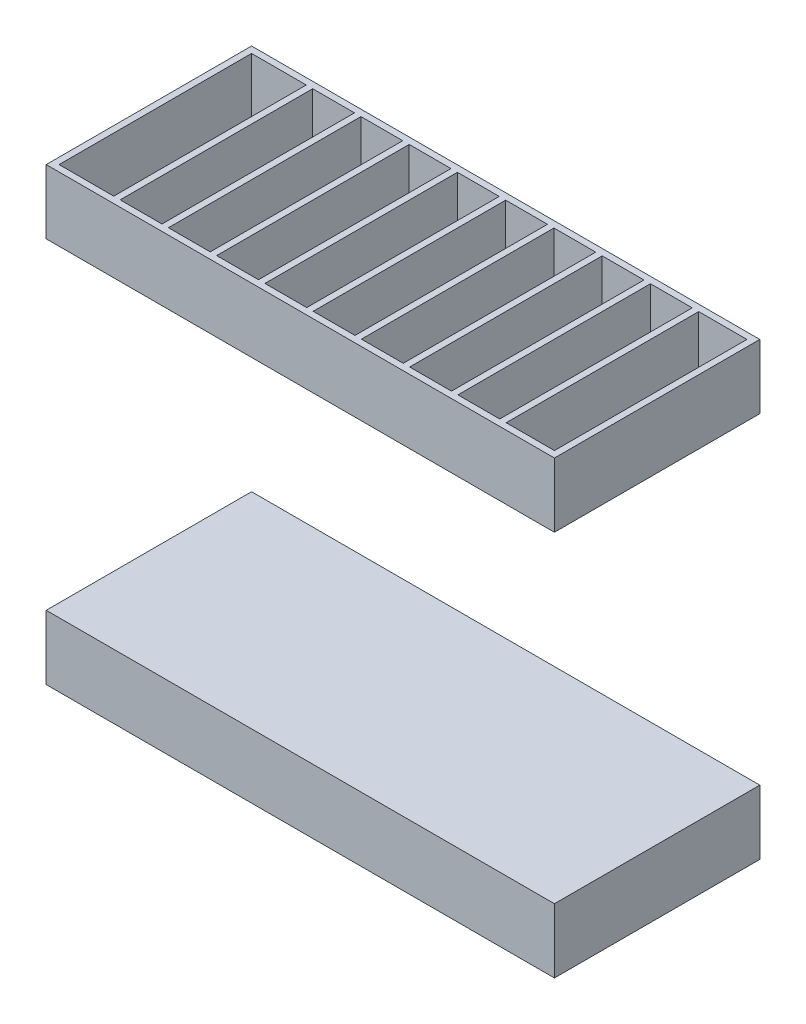
SolidWorks part; units mm, degrees
ref_plane "Front Plane" through (0, 0, 0) normal (0, 0, 1) x (1, 0, 0)
ref_plane "Top Plane" through (0, 0, 0) normal (0, 1, 0) x (1, 0, 0)
ref_plane "Right Plane" through (0, 0, 0) normal (1, 0, 0) x (0, 0, -1)
sketch "Sketch2" plane through (0, 0, 0) normal (0, 0, 1) x (1, 0, 0)
  line L0 (6022.8431, 33964.7267) -> (5722.8431, 33964.7267) construction
  line L1 (5002.5508, 33989.7267) -> (6582.5508, 33989.7267)
  line L2 (5002.5508, 33989.7267) -> (5002.5508, 33789.7267)
  line L3 (5002.5508, 33789.7267) -> (6582.5508, 33789.7267)
  line L4 (6582.5508, 33989.7267) -> (6582.5508, 33789.7267)
  line L6 (5857.8431, 33289.7267) -> (6727.5353, 33289.7267) construction
  line L8 (6582.5508, 32589.7267) -> (6582.5508, 32789.7267)
  line L9 (5002.5508, 32789.7267) -> (6582.5508, 32789.7267)
  line L10 (5002.5508, 32589.7267) -> (5002.5508, 32789.7267)
  line L11 (5002.5508, 32589.7267) -> (6582.5508, 32589.7267)
  dimension "D1" = 1580
  dimension "D2" = 200
  dimension "D3" = 500
  dimension "D4" = 25
extrude "Extrude1" add sketch "Sketch2" along normal up to surface (638.476 mm away)
shell "Shell1" thickness 20
shell "Shell2" thickness 20
sketch "Sketch3" plane through (0, 32769.7267, 0) normal (0, -1, 0) x (1, 0, 0)
  line L0 (5022.5508, 618.476) -> (6562.5508, 618.476) construction
  line L1 (5172.5508, 618.476) -> (5192.5508, 618.476)
  line L2 (5172.5508, 618.476) -> (5172.5508, 20)
  line L3 (5172.5508, 20) -> (5192.5508, 20)
  line L4 (5192.5508, 618.476) -> (5192.5508, 20)
  line L5 (6562.5508, 20) -> (5022.5508, 20) construction
  line L6 (5022.5508, 618.476) -> (5022.5508, 20) construction
  dimension "D1" = 20
  dimension "D2" = 150
extrude "Extrude2" add sketch "Sketch3" along normal up to surface (180 mm away) up to face at (5792.5508, 32589.7267, 319.238)
pattern_linear "LPattern1" count 9 spacing 150 along (1, 0, 0) of "Extrude2"
sketch "Sketch4" plane through (0, 33809.7267, 0) normal (0, 1, 0) x (1, 0, 0)
  line L0 (5022.5508, -20) -> (6562.5508, -20) construction
  line L1 (6412.5508, -20) -> (6392.5508, -20)
  line L2 (6412.5508, -20) -> (6412.5508, -618.476)
  line L3 (6412.5508, -618.476) -> (6392.5508, -618.476)
  line L4 (6392.5508, -20) -> (6392.5508, -618.476)
  line L5 (6562.5508, -618.476) -> (5022.5508, -618.476) construction
  dimension "D1" = 150
  dimension "D2" = 20
extrude "Extrude3" add sketch "Sketch4" along normal up to surface (180 mm away) up to face at (5792.5508, 33989.7267, 319.238)
pattern_linear "LPattern2" count 9 spacing 150 along (-1, 0, 0) of "Extrude3"
